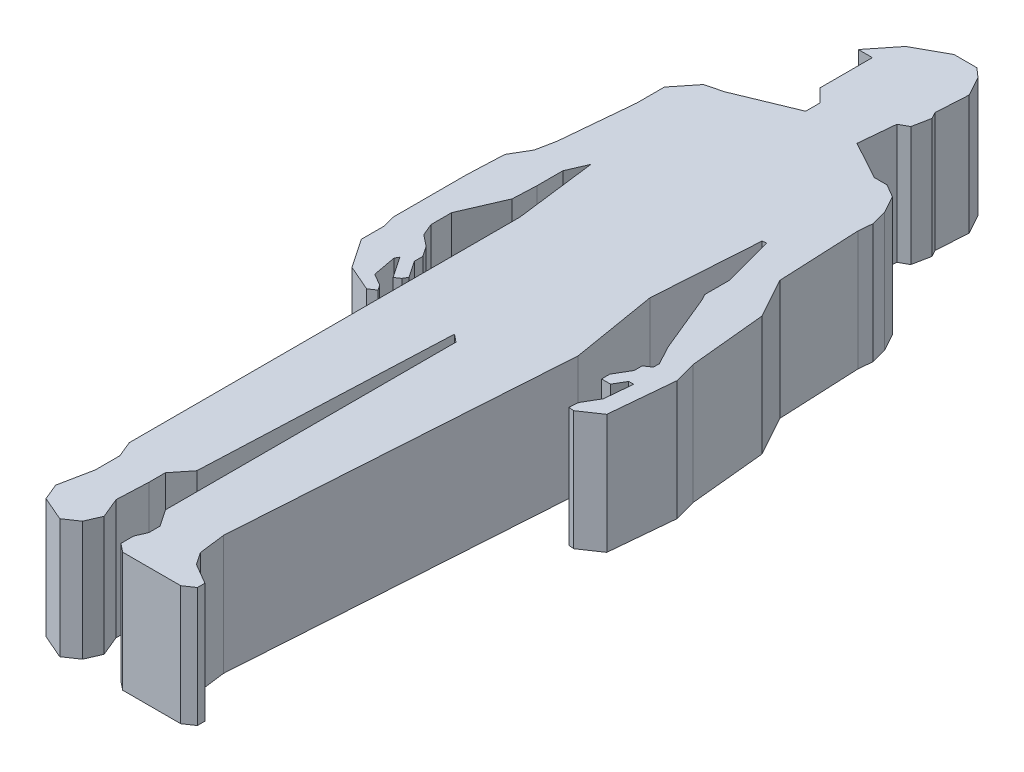
SolidWorks part; units mm, degrees
ref_plane "Front Plane" through (0, 0, 0) normal (0, 0, 1) x (1, 0, 0)
ref_plane "Top Plane" through (0, 0, 0) normal (0, 1, 0) x (1, 0, 0)
ref_plane "Right Plane" through (0, 0, 0) normal (1, 0, 0) x (0, 0, -1)
sketch "Sketch1" plane through (0, 0, 0) normal (0, 1, 0) x (1, 0, 0)
  line L0 (55, 316) -> (275, 316) construction
  line L1 (578.7014, 1825.2875) -> (531.1348, 1825.2875)
  line L2 (531.1348, 1825.2875) -> (465.9509, 1789.4658)
  line L3 (465.9509, 1789.4658) -> (421.9077, 1734.265)
  line L4 (421.9077, 1734.265) -> (451.2698, 1734.265)
  line L5 (451.2698, 1734.265) -> (451.2698, 1624.4507)
  line L6 (451.2698, 1624.4507) -> (478.5766, 1597.1439)
  line L7 (478.5766, 1597.1439) -> (478.5766, 1567.4881)
  line L8 (478.5766, 1567.4881) -> (359.0728, 1518.1598)
  line L9 (359.0728, 1518.1598) -> (323.251, 1508.7639)
  line L10 (323.251, 1508.7639) -> (287.1478, 1463.5146)
  line L11 (287.1478, 1463.5146) -> (287.1478, 1405.7151)
  line L12 (287.1478, 1405.7151) -> (273.108, 1253.8584)
  line L13 (273.108, 1253.8584) -> (265.025, 1213.4305)
  line L14 (265.025, 1213.4305) -> (242.3676, 1174.724)
  line L15 (242.3676, 1174.724) -> (239.0634, 1097.311)
  line L16 (239.0634, 1097.311) -> (239.0634, 944.8241)
  line L17 (239.0634, 944.8241) -> (245.8914, 918.7923)
  line L18 (245.8914, 918.7923) -> (245.8914, 871.1226)
  line L19 (245.8914, 871.1226) -> (287.1478, 810.2896)
  line L20 (287.1478, 810.2896) -> (341.1619, 786.8923)
  line L21 (341.1619, 786.8923) -> (355.4662, 796.5934)
  line L22 (355.4662, 796.5934) -> (348.314, 807.1394)
  line L23 (348.314, 807.1394) -> (323.251, 821.8104)
  line L24 (323.251, 821.8104) -> (314.1548, 871.1226)
  line L25 (314.1548, 871.1226) -> (318.7029, 878.8922)
  line L26 (318.7029, 878.8922) -> (348.314, 835.2303)
  line L27 (348.314, 835.2303) -> (359.0728, 842.5268)
  line L28 (359.0728, 842.5268) -> (364.6246, 852.0112)
  line L29 (364.6246, 852.0112) -> (341.1619, 886.6073)
  line L30 (341.1619, 886.6073) -> (341.1619, 904.3028)
  line L31 (341.1619, 904.3028) -> (326.5609, 925.832)
  line L32 (326.5609, 925.832) -> (302.7576, 944.8241)
  line L33 (302.7576, 944.8241) -> (292.1285, 970.5743)
  line L34 (292.1285, 970.5743) -> (292.1285, 1013.6769)
  line L35 (292.1285, 1013.6769) -> (330.422, 1102.0797)
  line L36 (330.422, 1102.0797) -> (332.5518, 1151.9794)
  line L37 (332.5518, 1151.9794) -> (332.5518, 1205.8078)
  line L38 (332.5518, 1205.8078) -> (350.2755, 1246.724)
  line L39 (350.2755, 1246.724) -> (371.6166, 1076.7859)
  line L40 (371.6166, 1076.7859) -> (371.6166, 895.4551)
  line L41 (371.6166, 895.4551) -> (371.6166, 260.0809)
  line L42 (371.6166, 260.0809) -> (385.4409, 226.5897)
  line L43 (385.4409, 226.5897) -> (385.4409, 175.3771)
  line L44 (385.4409, 175.3771) -> (371.6166, 106.2328)
  line L45 (371.6166, 106.2328) -> (385.8474, 71.7568)
  line L46 (385.8474, 71.7568) -> (436.5888, 49.7772)
  line L47 (436.5888, 49.7772) -> (464.9232, 68.9934)
  line L48 (464.9232, 68.9934) -> (478.5766, 100.513)
  line L49 (478.5766, 100.513) -> (460.9881, 143.1233)
  line L50 (460.9881, 143.1233) -> (463.8149, 209.351)
  line L51 (463.8149, 209.351) -> (463.8149, 243.3353)
  line L52 (463.8149, 243.3353) -> (493.0371, 279.9604)
  line L53 (493.0371, 279.9604) -> (515.0885, 796.5934)
  line L54 (515.0885, 796.5934) -> (531.1348, 783.7905)
  line L55 (531.1348, 783.7905) -> (531.1348, 176.2371)
  line L56 (531.1348, 176.2371) -> (554.9181, 141.1684)
  line L57 (554.9181, 141.1684) -> (554.9181, 117.6771)
  line L58 (554.9181, 117.6771) -> (545.299, 95.4708)
  line L59 (545.299, 95.4708) -> (545.299, 68.9934)
  line L60 (545.299, 68.9934) -> (562.9423, 54.9163)
  line L61 (562.9423, 54.9163) -> (684.3515, 54.9163)
  line L62 (684.3515, 54.9163) -> (705.1083, 68.9934)
  line L63 (705.1083, 68.9934) -> (705.1083, 84.7532)
  line L64 (705.1083, 84.7532) -> (662.2565, 109.8372)
  line L65 (662.2565, 109.8372) -> (645.0091, 135.2687)
  line L66 (645.0091, 135.2687) -> (637.9794, 191.2459)
  line L67 (637.9794, 191.2459) -> (683.6824, 886.6073)
  line L68 (683.6824, 886.6073) -> (653.6328, 1066.725)
  line L69 (653.6328, 1066.725) -> (668.0865, 1286.6351)
  line L70 (668.0865, 1286.6351) -> (676.5721, 1288.0508)
  line L71 (676.5721, 1288.0508) -> (705.0729, 1181.8095)
  line L72 (705.0729, 1181.8095) -> (705.0729, 1129.7757)
  line L73 (705.0729, 1129.7757) -> (711.8474, 1117.4484)
  line L74 (711.8474, 1117.4484) -> (762.5101, 994.7118)
  line L75 (762.5101, 994.7118) -> (782.8504, 957.6992)
  line L76 (782.8504, 957.6992) -> (782.8504, 944.8241)
  line L77 (782.8504, 944.8241) -> (768.8484, 935.3281)
  line L78 (768.8484, 935.3281) -> (768.8484, 918.7923)
  line L79 (768.8484, 918.7923) -> (750.0084, 886.6073)
  line L80 (750.0084, 886.6073) -> (750.0084, 869.3093)
  line L81 (750.0084, 869.3093) -> (768.8484, 869.3093)
  line L82 (768.8484, 869.3093) -> (782.8504, 893.2293)
  line L83 (782.8504, 893.2293) -> (793.2146, 893.2293)
  line L84 (793.2146, 893.2293) -> (787.8523, 835.2303)
  line L85 (787.8523, 835.2303) -> (768.8484, 802.7653)
  line L86 (768.8484, 802.7653) -> (767.0941, 783.7905)
  line L87 (767.0941, 783.7905) -> (778.3504, 782.7498)
  line L88 (778.3504, 782.7498) -> (819.5353, 810.6812)
  line L89 (819.5353, 810.6812) -> (831.9374, 944.8241)
  line L90 (831.9374, 944.8241) -> (819.5353, 991.0548)
  line L91 (819.5353, 991.0548) -> (803.8158, 1150.6715)
  line L92 (803.8158, 1150.6715) -> (757.8649, 1234.2869)
  line L93 (757.8649, 1234.2869) -> (750.0084, 1405.7151)
  line L94 (750.0084, 1405.7151) -> (752.6803, 1434.6149)
  line L95 (752.6803, 1434.6149) -> (743.9568, 1467.133)
  line L96 (743.9568, 1467.133) -> (724.0628, 1503.3337)
  line L97 (724.0628, 1503.3337) -> (697.0283, 1519.1587)
  line L98 (697.0283, 1519.1587) -> (670.6291, 1519.1587)
  line L99 (670.6291, 1519.1587) -> (590.4645, 1562.8918)
  line L100 (590.4645, 1562.8918) -> (597.5298, 1639.3117)
  line L101 (597.5298, 1639.3117) -> (616.2534, 1649.6013)
  line L102 (616.2534, 1649.6013) -> (623.6469, 1686.5808)
  line L103 (623.6469, 1686.5808) -> (616.2534, 1700.0346)
  line L104 (616.2534, 1700.0346) -> (620.1764, 1767.8394)
  line L105 (620.1764, 1767.8394) -> (597.5298, 1808.8928)
  line L106 (597.5298, 1808.8928) -> (578.7014, 1825.2875)
  dimension "D1" = 1770.3713
extrude "Boss-Extrude1" add sketch "Sketch1" along normal blind 250
ref_plane "Plane1" through (0, 130, 0) normal (0, 1, 0) x (1, 0, 0)
sketch "Sketch2" plane through (0, 130, 0) normal (0, 1, 0) x (1, 0, 0)
  line L0 (532.5824, -40.8344) -> (532.5824, 2359.1656)
